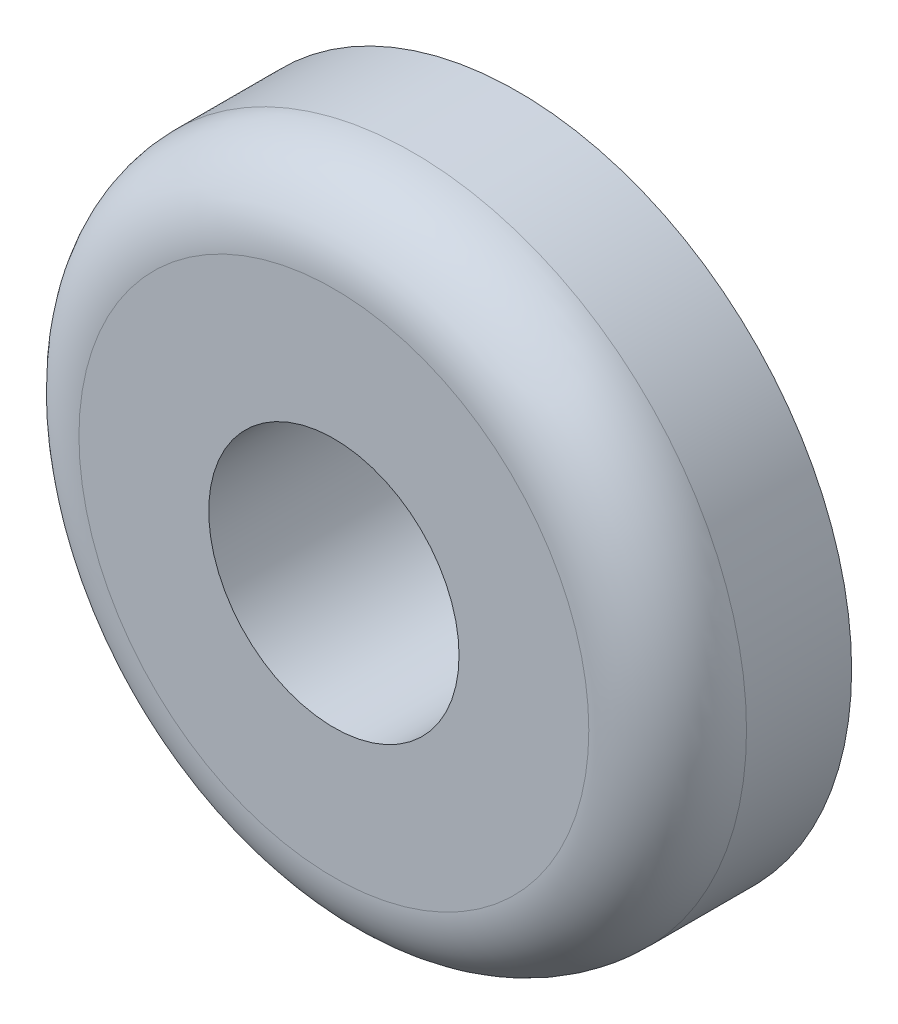
SolidWorks part; units mm, degrees
ref_plane "Front Plane" through (0, 0, 0) normal (0, 0, 1) x (1, 0, 0)
ref_plane "Top Plane" through (0, 0, 0) normal (0, 1, 0) x (1, 0, 0)
ref_plane "Right Plane" through (0, 0, 0) normal (1, 0, 0) x (0, 0, -1)
sketch "Sketch1" plane through (0, 0, 0) normal (0, 0, 1) x (1, 0, 0)
  circle A0 centre (0, 0) radius 6.35
  circle A1 centre (0, 0) radius 2.3813
  dimension "D1" = 4.7625
  dimension "D2" = 12.7
extrude "Boss-Extrude1" add sketch "Sketch1" along normal blind 3.5
fillet "Fillet1" radius 1.5 1 edges at (6.35, 0, 3.5)
